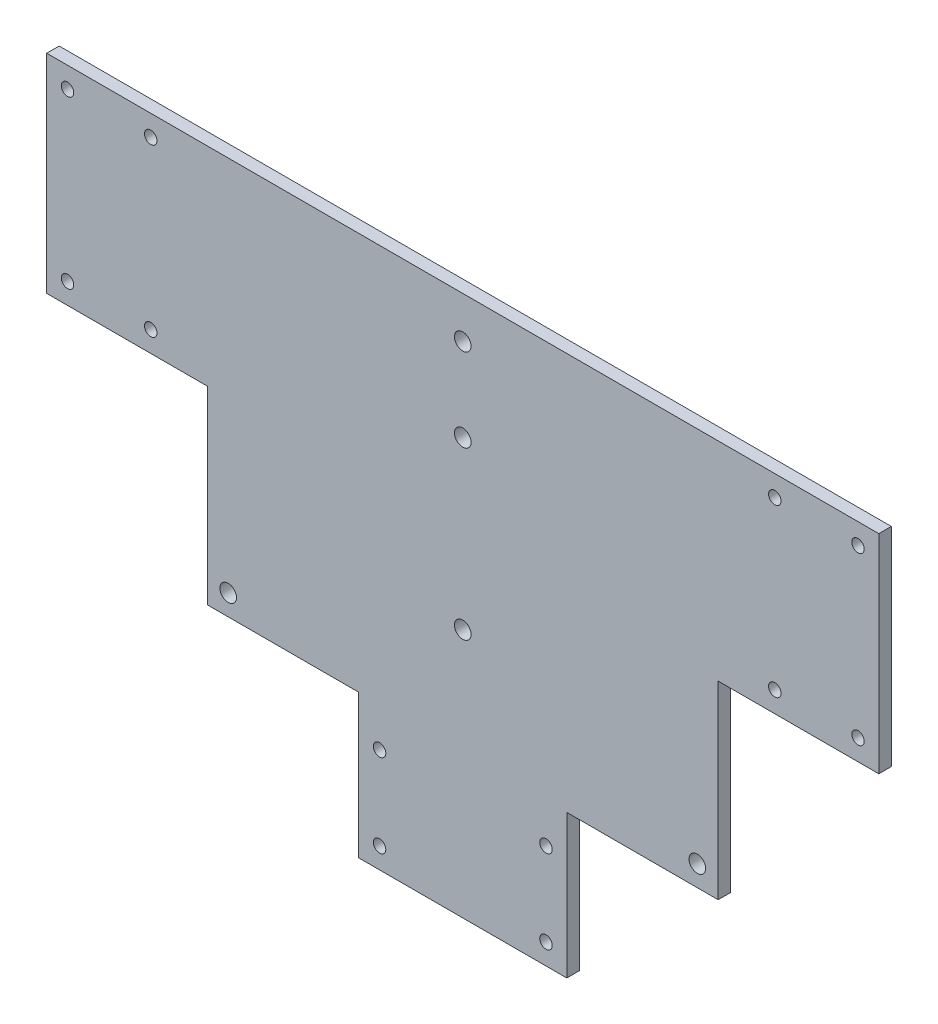
SolidWorks part; units mm, degrees
ref_plane "Plan de face" through (0, 0, 0) normal (0, 0, 1) x (1, 0, 0)
ref_plane "Plan de dessus" through (0, 0, 0) normal (0, 1, 0) x (1, 0, 0)
ref_plane "Plan de droite" through (0, 0, 0) normal (1, 0, 0) x (0, 0, -1)
sketch "Esquisse1" plane through (0, 0, 0) normal (0, 0, 1) x (1, 0, 0)
  line L0 (-25, 0) -> (25, 0) construction
  line L1 (0, 50) -> (-100, 50)
  line L2 (25, -80) -> (25, -45.5212)
  line L3 (-70, 50) -> (-70, 0) construction
  line L4 (25, -80) -> (-25, -80)
  line L5 (-25, -50) -> (25, -50) construction
  line L6 (-25, -65) -> (25, -65) construction
  line L7 (-25, -80) -> (-25, -45.5212)
  line L8 (0, 50) -> (0, -80) construction
  line L9 (-85, 50) -> (-85, 0) construction
  line L10 (0, 50) -> (100, 50)
  line L11 (100, 50) -> (100, 0)
  line L12 (100, 0) -> (61.3816, 0)
  line L13 (-100, 50) -> (-100, 0)
  line L14 (-100, 0) -> (-61.3816, 0)
  line L15 (61.3816, 0) -> (25, 0) construction
  line L16 (-100, 25) -> (-70, 25) construction
  line L17 (-25, -45.5212) -> (-25, 0) construction
  line L18 (-61.3816, 0) -> (-61.3816, -45.5212)
  line L19 (-61.3816, -45.5212) -> (-25, -45.5212)
  line L20 (0, -20) -> (-25, -20) construction
  line L21 (25, -45.5212) -> (25, 0) construction
  line L22 (61.3816, 0) -> (61.3816, -45.5212)
  line L23 (61.3816, -45.5212) -> (25, -45.5212)
  line L24 (0, -20) -> (-56.3816, -40.5212) construction
  circle A0 centre (0, 20) radius 2
  circle A1 centre (0, -20) radius 2
  circle A2 centre (0, 40) radius 2
  circle A3 centre (-20, -55) radius 1.5
  circle A4 centre (20, -55) radius 1.5
  circle A5 centre (20, -75) radius 1.5
  circle A6 centre (-20, -75) radius 1.5
  circle A7 centre (-95, 45) radius 1.5
  circle A8 centre (-75, 45) radius 1.5
  circle A9 centre (-75, 5) radius 1.5
  circle A10 centre (-95, 5) radius 1.5
  circle A11 centre (75, 5) radius 1.5
  circle A12 centre (95, 5) radius 1.5
  circle A13 centre (75, 45) radius 1.5
  circle A14 centre (95, 45) radius 1.5
  circle A15 centre (56.3816, -40.5212) radius 2
  circle A17 centre (-56.3816, -40.5212) radius 2
  point P0 (0, 0)
  point P2 (0, 0)
  dimension "D3" = 4
  dimension "D4" = 4
  dimension "D5" = 20
  dimension "D7" = 4
  dimension "D13" = 3
  dimension "D14" = 20
  dimension "D19" = 3
  dimension "D20" = 10
  dimension "D21" = 20
  dimension "D22" = 5
  dimension "D23" = 5
  dimension "D24" = 60
  dimension "D25" = 20
  dimension "D26" = 4
  dimension "D27" = 25
  dimension "D6" = 20
  dimension "D8" = 40
  dimension "D9" = 80
  dimension "D10" = 30
  dimension "D11" = 30
  dimension "D12" = 15
  dimension "D15" = 10
  dimension "D16" = 100
  dimension "D17" = 50
  dimension "D18" = 15
extrude "Boss.-Extru.1" add sketch "Esquisse1" along normal blind 3
